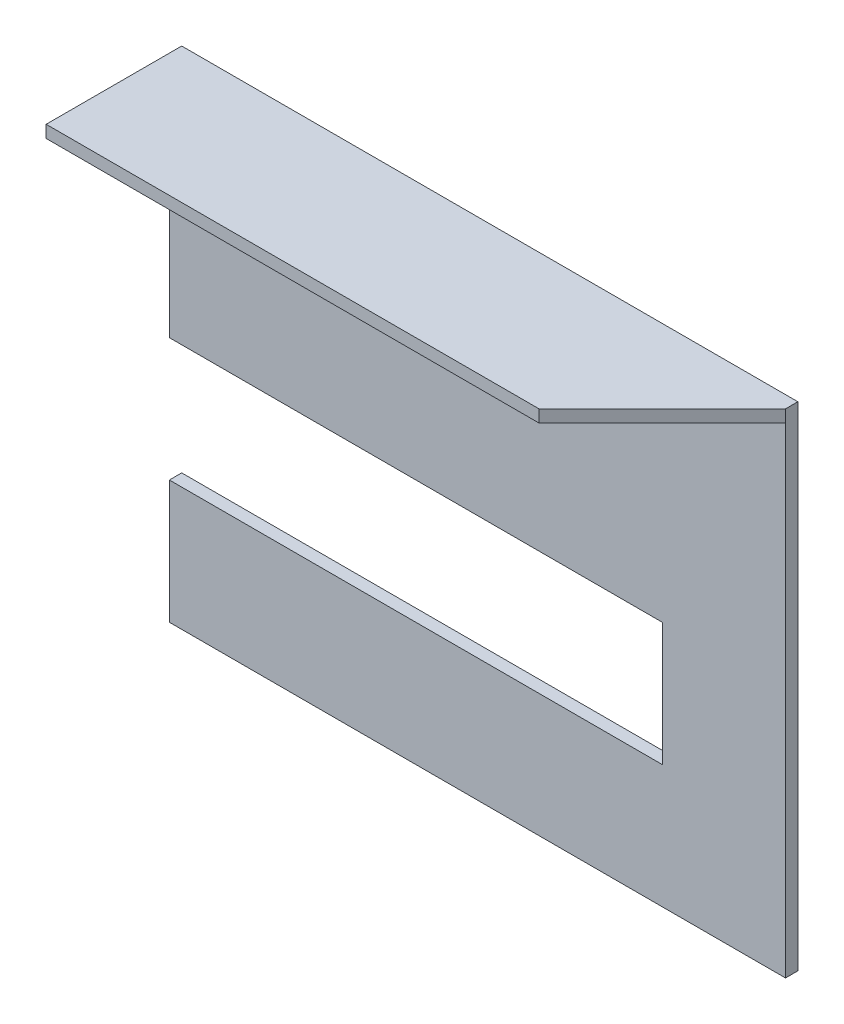
SolidWorks part; units mm, degrees
ref_plane "前视基准面" through (0, 0, 0) normal (0, 0, 1) x (1, 0, 0)
ref_plane "上视基准面" through (0, 0, 0) normal (0, 1, 0) x (1, 0, 0)
ref_plane "右视基准面" through (0, 0, 0) normal (1, 0, 0) x (0, 0, -1)
sketch "草图1" plane through (0, 0, 0) normal (0, 0, 1) x (1, 0, 0)
  line L0 (23.4968, -8.3326) -> (23.4968, -17.8648)
  line L1 (-26.5032, 9.3987) -> (23.4968, 9.3987)
  line L2 (-26.5032, 9.3987) -> (-26.5032, -10.6013)
  line L3 (-26.5032, -10.6013) -> (13.4968, -10.6013)
  line L4 (23.4968, 9.3987) -> (23.4968, -8.3326)
  line L5 (-26.5032, 9.3987) -> (23.4968, -8.3326) construction
  line L6 (-26.5032, -10.6013) -> (23.4968, 9.3987) construction
  line L7 (13.4968, -20.6013) -> (-26.5032, -20.6013)
  line L8 (-26.5032, -20.6013) -> (-26.5032, -30.6013)
  line L9 (-26.5032, -30.6013) -> (23.4968, -30.6013)
  line L10 (23.4968, -30.6013) -> (23.4968, -17.8648)
  line L11 (13.4968, -10.6013) -> (13.4968, -20.6013)
  point P0 (0, 0)
  dimension "D1" = 10
  dimension "D2" = 40
extrude "凸台-拉伸1" add sketch "草图1" along normal blind 1
sketch "草图2" plane through (0, 0, 1) normal (0, 0, 1) x (1, 0, 0)
  line L0 (-26.5032, 9.3987) -> (23.4968, 9.3987)
  line L1 (23.4968, 9.3987) -> (23.4968, 8.3987)
  line L2 (23.4968, -30.6013) -> (23.4968, 9.3987) construction
  line L3 (23.4968, 8.3987) -> (-26.5032, 8.3987)
  line L4 (-26.5032, 9.3987) -> (-26.5032, -10.6013) construction
  line L5 (-26.5032, 8.3987) -> (-26.5032, 9.3987)
extrude "凸台-拉伸2" add sketch "草图2" along normal blind 10
chamfer "倒角1" distance 10 angle 45 1 edges at (23.4968, 8.8987, 11)
